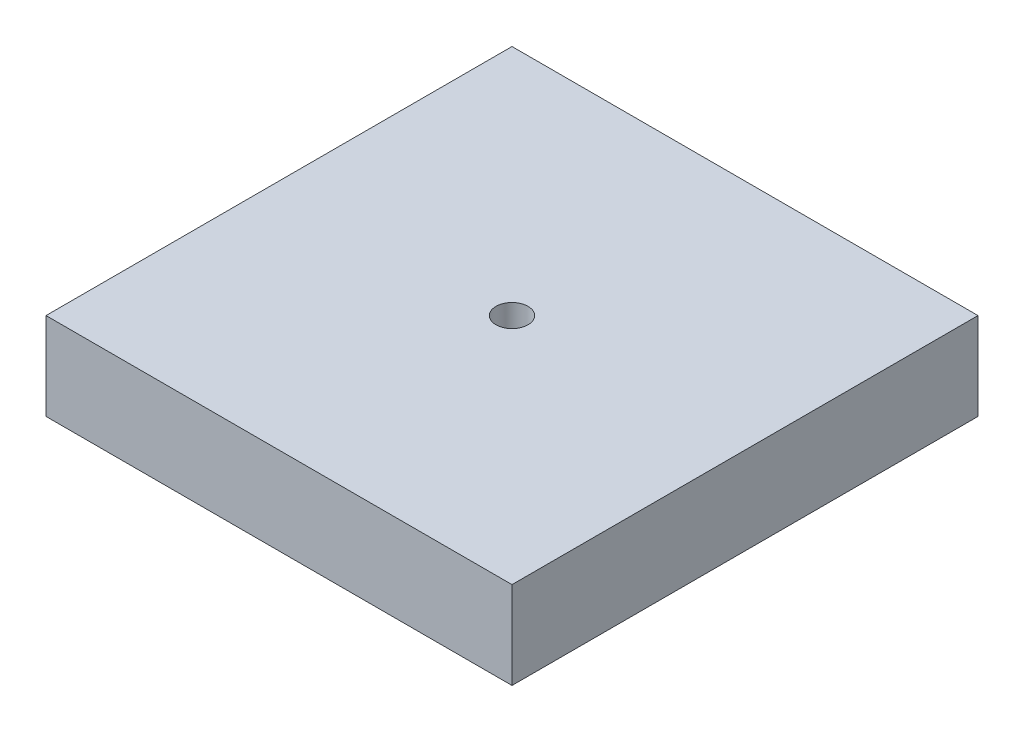
SolidWorks part; units mm, degrees
ref_plane "Front" through (0, 0, 0) normal (0, 0, 1) x (1, 0, 0)
ref_plane "Top" through (0, 0, 0) normal (0, 1, 0) x (1, 0, 0)
ref_plane "Right" through (0, 0, 0) normal (1, 0, 0) x (0, 0, -1)
sketch "Sketch1" plane through (0, 0, 0) normal (0, 1, 0) x (1, 0, 0)
  line L1 (50.8, 50.8) -> (-50.8, 50.8)
  line L2 (50.8, 50.8) -> (50.8, -50.8)
  line L3 (50.8, -50.8) -> (-50.8, -50.8)
  line L4 (-50.8, 50.8) -> (-50.8, -50.8)
  line L5 (50.8, 50.8) -> (-50.8, -50.8) construction
  line L6 (50.8, -50.8) -> (-50.8, 50.8) construction
  point P0 (0, 0)
  dimension "D1" = 101.6
extrude "Boss-Extrude1" add sketch "Sketch1" along normal blind 19.05
sketch "Sketch2" plane through (0, 19.05, 0) normal (0, 1, 0) x (1, 0, 0)
  line L4 (-50.8, 50.8) -> (-50.8, -50.8)
  line L5 (-50.8, -50.8) -> (50.8, -50.8)
  line L6 (50.8, -50.8) -> (50.8, 50.8)
  line L7 (50.8, 50.8) -> (-50.8, 50.8)
  line L8 (-50.8, 50.8) -> (-50.8, -50.8)
  line L9 (-50.8, -50.8) -> (50.8, -50.8)
  line L10 (50.8, -50.8) -> (50.8, 50.8)
  line L11 (50.8, 50.8) -> (-50.8, 50.8)
  circle A1 centre (0, 0) radius 3.4925
  dimension "D4" = 6.985
  dimension "D2" = 50.8
  dimension "D3" = 50.8
  dimension "D1" = 0
extrude "Cut-Extrude1" cut sketch "Sketch2" against normal through all both and the other way through all contours A1
